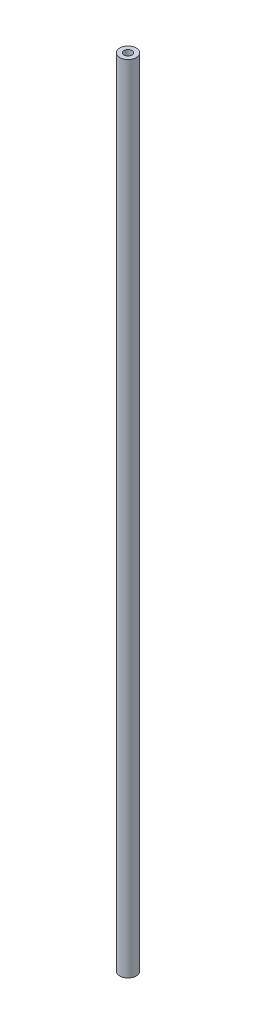
SolidWorks part; units mm, degrees
material "6061 Alloy"
ref_plane "Front Plane" through (0, 0, 0) normal (0, 0, 1) x (1, 0, 0)
ref_plane "Top Plane" through (0, 0, 0) normal (0, 1, 0) x (1, 0, 0)
ref_plane "Right Plane" through (0, 0, 0) normal (1, 0, 0) x (0, 0, -1)
sketch "Sketch1" plane through (0, 0, 0) normal (0, 1, 0) x (1, 0, 0)
  circle A0 centre (0, 0) radius 3.175
  circle A1 centre (0, 0) radius 1.524
  dimension "D1" = 6.35
  dimension "D2" = 3.048
extrude "Boss-Extrude1" add sketch "Sketch1" along normal blind 304.8
